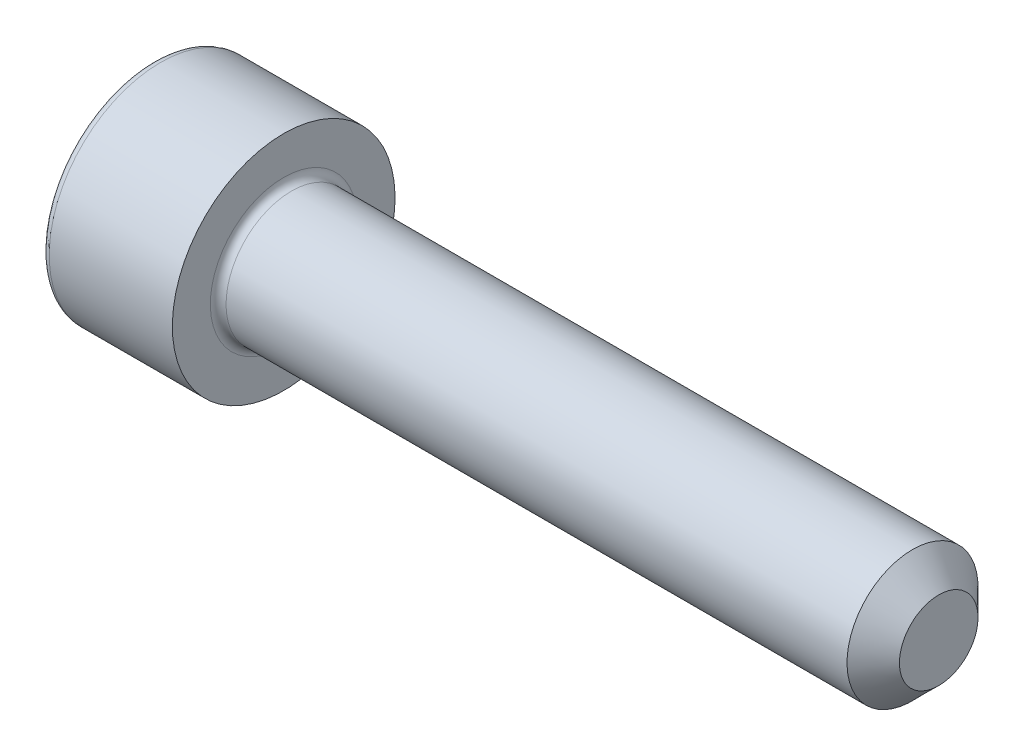
SolidWorks part; units mm, degrees
ref_plane "Спереди" through (0, 0, 0) normal (0, 0, 1) x (1, 0, 0)
ref_plane "Сверху" through (0, 0, 0) normal (0, 1, 0) x (1, 0, 0)
ref_plane "Справа" through (0, 0, 0) normal (1, 0, 0) x (0, 0, -1)
sketch "Эскиз1" plane through (0, 0, 0) normal (0, 0, 1) x (1, 0, 0)
  line L0 (0, 0) -> (0, 4.25)
  line L1 (0, 4.25) -> (5, 4.25)
  line L2 (5, 4.25) -> (5, 2.5)
  line L3 (5, 2.5) -> (30, 2.5)
  line L4 (30, 2.5) -> (30, 0)
  line L5 (30, 0) -> (0, 0) construction
  line L6 (0, 0) -> (30, 0)
  dimension "D1" = 8.5
  dimension "D2" = 5
  dimension "D3" = 5
  dimension "D4" = 25
revolve "Повернуть1" add sketch "Эскиз1" angle 360 about L5
cosmetic thread "Условное изображение резьбы1" parameters "D2"=4.11
sketch "Эскиз2" plane through (0, 0, 0) normal (-1, 0, 0) x (0, 0, 1)
  line L1 (-1.1547, 2) -> (-2.3094, 0)
  line L2 (-2.3094, 0) -> (-1.1547, -2)
  line L3 (-1.1547, -2) -> (1.1547, -2)
  line L4 (1.1547, -2) -> (2.3094, 0)
  line L5 (2.3094, 0) -> (1.1547, 2)
  line L6 (1.1547, 2) -> (-1.1547, 2)
  circle A0 centre (0, 0) radius 2 construction
  dimension "D1" = 4
extrude "Вырез-Вытянуть1" cut sketch "Эскиз2" against normal blind 2.5
fillet "Скругление1" radius 0.3 2 edges at (0, 4.25, 0) (5, 2.5, 0)
chamfer "Фаска1" distance 1 angle 45 1 edges at (30, 2.5, 0)
